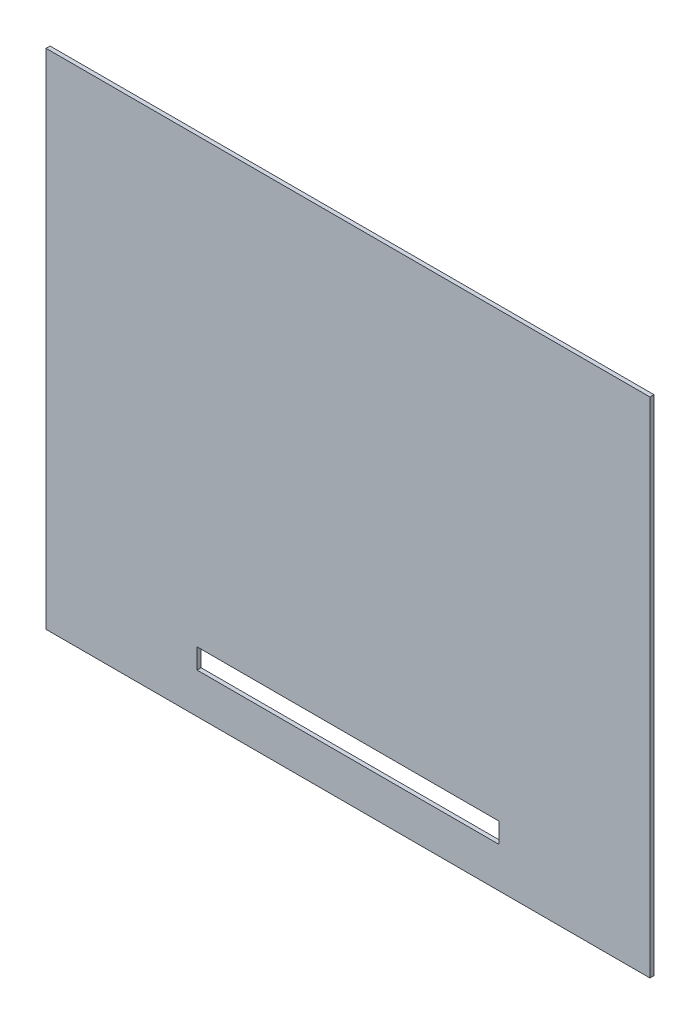
SolidWorks part; units mm, degrees
ref_plane "Front Plane" through (0, 0, 0) normal (0, 0, 1) x (1, 0, 0)
ref_plane "Top Plane" through (0, 0, 0) normal (0, 1, 0) x (1, 0, 0)
ref_plane "Right Plane" through (0, 0, 0) normal (1, 0, 0) x (0, 0, -1)
sketch "Sketch1" plane through (0, 0, 0) normal (0, 0, 1) x (1, 0, 0)
  line L0 (-150, 0) -> (0, 0) construction
  line L1 (-150, 125) -> (150, 125)
  line L2 (-150, 125) -> (-150, -125)
  line L3 (-150, -125) -> (150, -125)
  line L4 (150, 125) -> (150, -125)
  line L5 (0, 0) -> (0, -125) construction
  dimension "D2" = 300
  dimension "D3" = 250
extrude "Boss-Extrude1" add sketch "Sketch1" along normal blind 2
sketch "Sketch4" plane through (0, 0, 2) normal (0, 0, 1) x (1, 0, 0)
  line L0 (-150, 125) -> (-150, -125) construction
  line L1 (142.5, 117.5) -> (-142.5, 117.5)
  line L2 (142.5, 117.5) -> (142.5, -117.5)
  line L3 (142.5, -117.5) -> (-142.5, -117.5)
  line L4 (-142.5, 117.5) -> (-142.5, -117.5)
  line L5 (142.5, 117.5) -> (-142.5, -117.5) construction
  line L6 (142.5, -117.5) -> (-142.5, 117.5) construction
  line L7 (150, 125) -> (-150, 125) construction
  line L8 (-142.5, -98) -> (142.5, -98) construction
  line L9 (-150, -125) -> (150, -125) construction
  line L11 (-142.5, 0) -> (142.5, 0) construction
  point P0 (0, 0)
  point P11 (142.5, 98)
  point P12 (-142.5, 0)
  point P13 (-142.5, -98)
  point P15 (142.5, 0)
  point P16 (-142.5, 98)
  point P17 (142.5, -98)
  dimension "D1" = 7.5
  dimension "D2" = 7.5
  dimension "D3" = 27
sketch "Sketch5" plane through (0, 0, 0) normal (0, 0, -1) x (-1, 0, 0)
  line L0 (0, 0) -> (0, -100) construction
  line L1 (-75, -95) -> (75, -95)
  line L2 (-75, -95) -> (-75, -105)
  line L3 (-75, -105) -> (75, -105)
  line L4 (75, -95) -> (75, -105)
  line L5 (-75, -95) -> (75, -105) construction
  line L6 (-75, -105) -> (75, -95) construction
  line L7 (150, -125) -> (-150, -125) construction
  point P0 (0, -100)
  dimension "D1" = 10
  dimension "D2" = 20
  dimension "D3" = 150
extrude "Cut-Extrude1" cut sketch "Sketch5" against normal through all
